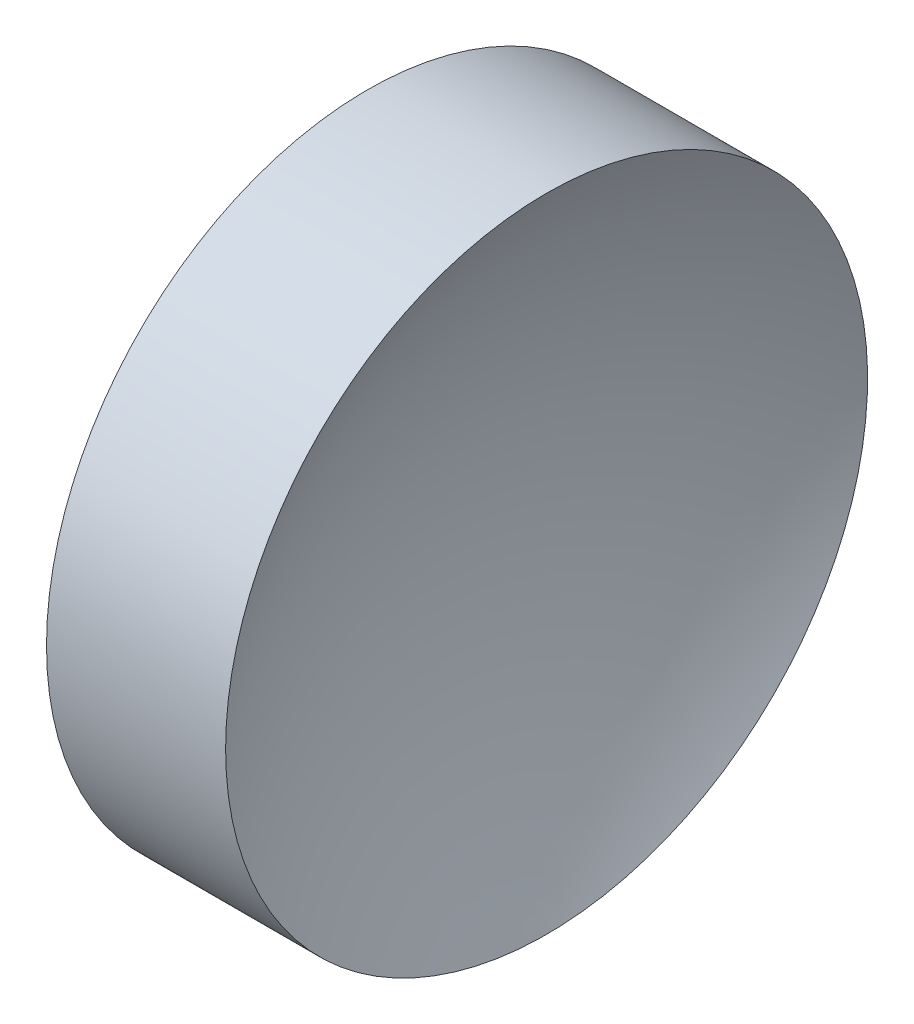
SolidWorks part; units mm, degrees
ref_plane "前视基准面" through (0, 0, 0) normal (0, 0, 1) x (1, 0, 0)
ref_plane "上视基准面" through (0, 0, 0) normal (0, 1, 0) x (1, 0, 0)
ref_plane "右视基准面" through (0, 0, 0) normal (1, 0, 0) x (0, 0, -1)
sketch "草图1" plane through (0, 0, 0) normal (0, 0, 1) x (1, 0, 0)
  line L0 (42.4499, 26.089) -> (50.324, 26.089) construction
  line L1 (44.3196, 26.089) -> (44.3196, 31.089)
  line L2 (45.8196, 26.089) -> (44.3196, 26.089)
  line L3 (44.3196, 31.089) -> (47.1096, 31.089)
  arc A0 (47.1096, 31.089) -> (45.8196, 26.089) centre (56.1545, 26.089) ccw
revolve "旋转1" add sketch "草图1" angle 360 about L0
